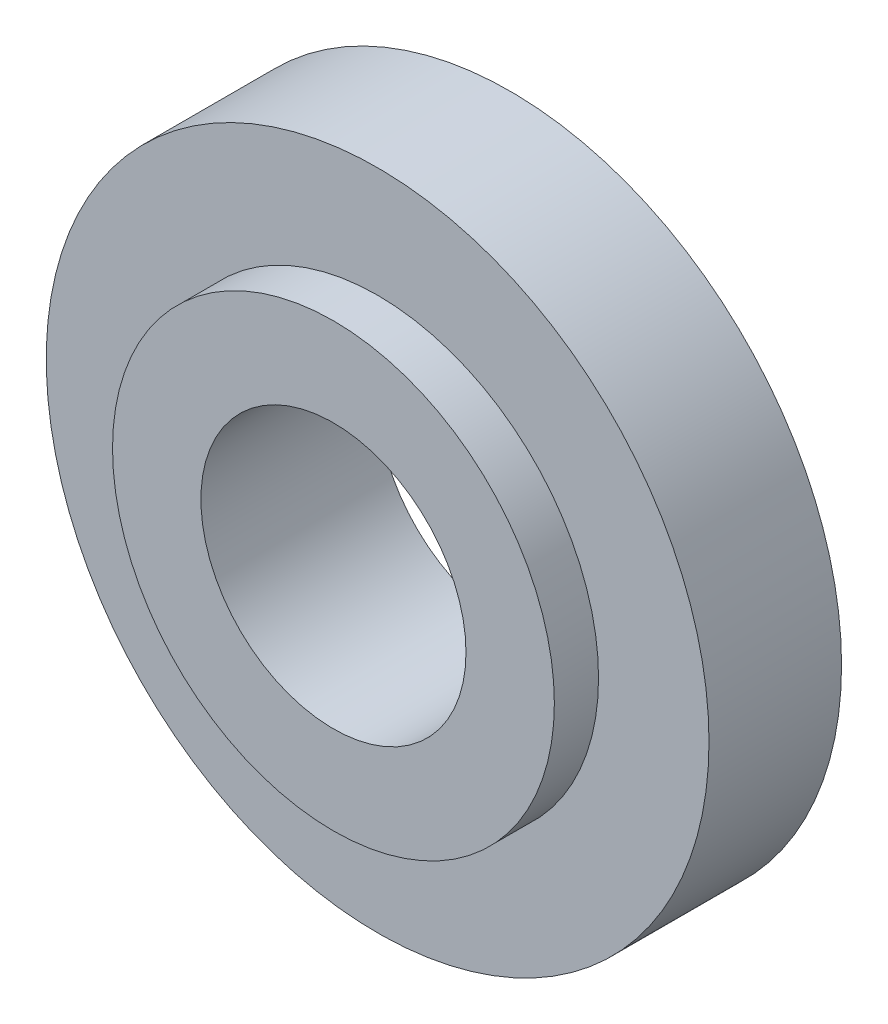
SolidWorks part; units mm, degrees
ref_plane "Front Plane" through (0, 0, 0) normal (0, 0, 1) x (1, 0, 0)
ref_plane "Top Plane" through (0, 0, 0) normal (0, 1, 0) x (1, 0, 0)
ref_plane "Right Plane" through (0, 0, 0) normal (1, 0, 0) x (0, 0, -1)
sketch "Sketch1" plane through (0, 0, 0) normal (0, 0, 1) x (1, 0, 0)
  circle A0 centre (0, 0) radius 3.75
  circle A1 centre (0, 0) radius 1.5
  dimension "D1" = 7.5
  dimension "D2" = 3
extrude "Boss-Extrude1" add sketch "Sketch1" along normal blind 1.5
sketch "Sketch2" plane through (0, 0, 1.5) normal (0, 0, 1) x (1, 0, 0)
  circle A0 centre (0, 0) radius 2.5
  circle A1 centre (0, 0) radius 1.5 construction
  circle A2 centre (0, 0) radius 1.5
  dimension "D1" = 5
extrude "Boss-Extrude2" add sketch "Sketch2" along normal blind 0.5
scale "Scale1" bodies to scale 102 scale about centroid uniform scaling yes scale factor 2
